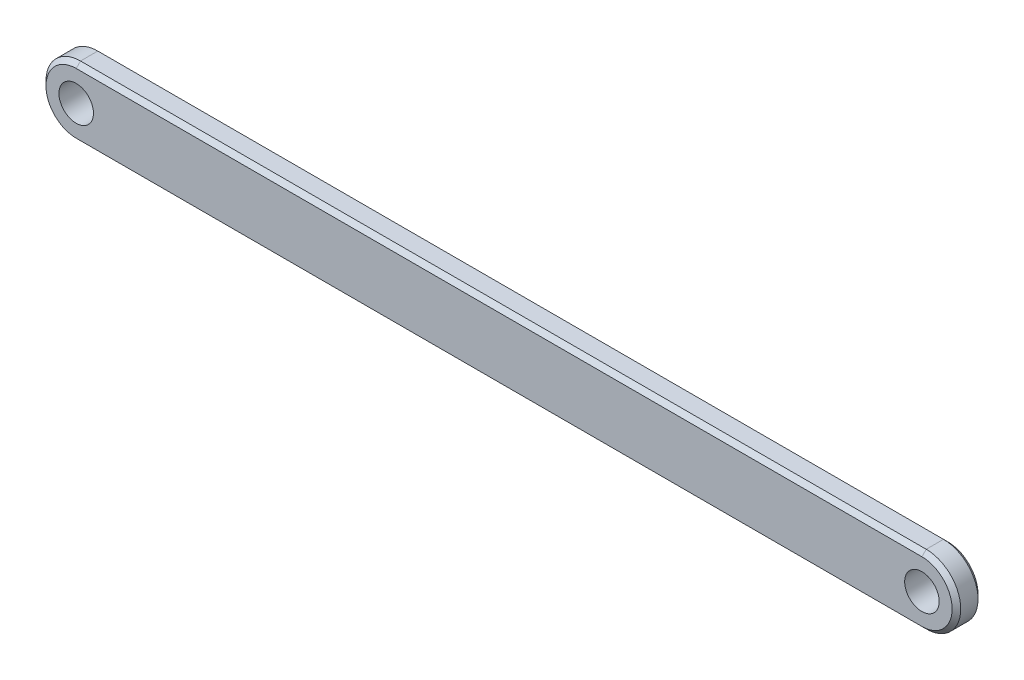
SolidWorks part; units mm, degrees
ref_plane "Front Plane" through (0, 0, 0) normal (0, 0, 1) x (1, 0, 0)
ref_plane "Top Plane" through (0, 0, 0) normal (0, 1, 0) x (1, 0, 0)
ref_plane "Right Plane" through (0, 0, 0) normal (1, 0, 0) x (0, 0, -1)
sketch "Sketch1" plane through (0, 0, 0) normal (0, 0, 1) x (1, 0, 0)
  line L0 (-11.0194, 0) -> (86.9806, 0) construction
  line L1 (-11.0194, 4) -> (86.9806, 4)
  line L2 (-11.0194, -4) -> (86.9806, -4)
  arc A0 (-11.0194, 4) -> (-11.0194, -4) centre (-11.0194, 0) ccw
  arc A1 (86.9806, -4) -> (86.9806, 4) centre (86.9806, 0) ccw
  circle A2 centre (-11.0194, 0) radius 2
  circle A3 centre (86.9806, 0) radius 2
  point P3 (37.9806, 0)
  dimension "D1" = 8
  dimension "D2" = 98
extrude "Boss-Extrude1" add sketch "Sketch1" along normal blind 3
chamfer "Chamfer1" distance 0.5 angle 45 8 edges at (37.9806, 4, 0) (-15.0194, 0, 0) (90.9806, 0, 0) (37.9806, -4, 0) (37.9806, -4, 3) (90.9806, 0, 3) (-15.0194, 0, 3) (37.9806, 4, 3)
